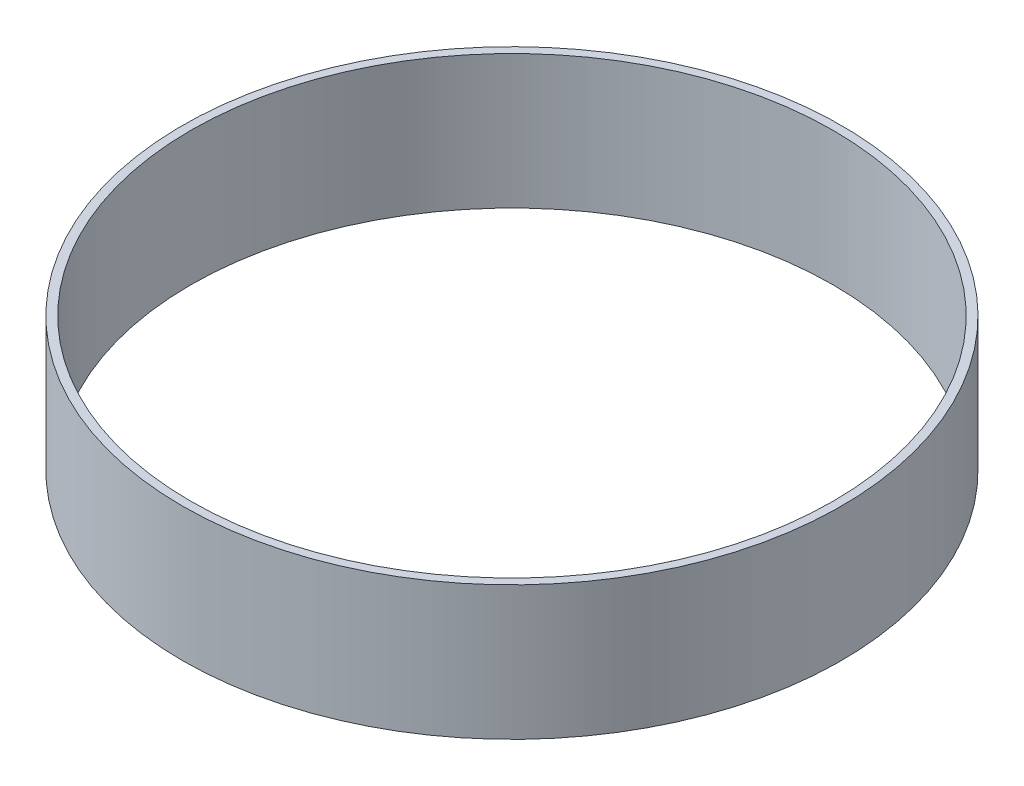
SolidWorks part; units mm, degrees
material "ABS PC"
ref_plane "Front" through (0, 0, 0) normal (0, 0, 1) x (1, 0, 0)
ref_plane "Top" through (0, 0, 0) normal (0, 1, 0) x (1, 0, 0)
ref_plane "Right" through (0, 0, 0) normal (1, 0, 0) x (0, 0, -1)
sketch "Sketch1" plane through (0, 0, 0) normal (0, 1, 0) x (1, 0, 0)
  circle A0 centre (0, 0) radius 96
  circle A1 centre (0, 0) radius 98.5
  dimension "D1" = 2.5
  dimension "D2" = 192
extrude "Boss-Extrude1" add sketch "Sketch1" along normal blind 40
sketch "Sketch2" plane through (0, 0, 0) normal (0, 0, 1) x (1, 0, 0)
  line L0 (0, 0) -> (0, 5) construction
  circle A0 centre (0, 5) radius 2.5
  dimension "D2" = 5
  dimension "D1" = 5
